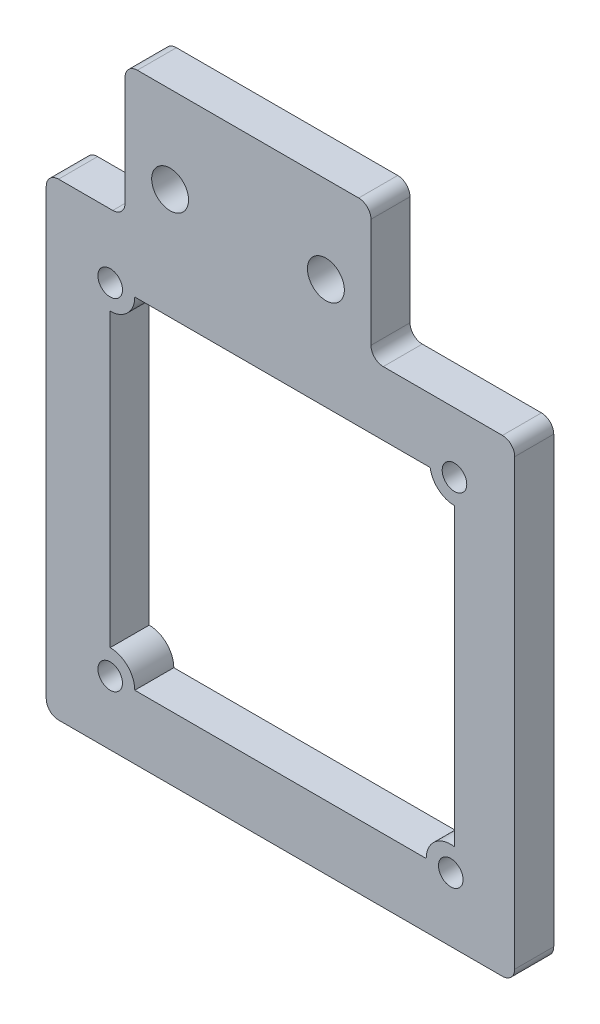
SolidWorks part; units mm, degrees
ref_plane "Front Plane" through (0, 0, 0) normal (0, 0, 1) x (1, 0, 0)
ref_plane "Top Plane" through (0, 0, 0) normal (0, 1, 0) x (1, 0, 0)
ref_plane "Right Plane" through (0, 0, 0) normal (1, 0, 0) x (0, 0, -1)
sketch "Sketch1" plane through (0, 0, 0) normal (0, 0, 1) x (1, 0, 0)
  line L0 (31.6909, -38.1) -> (31.6909, 0) construction
  line L1 (-6.4091, -38.1) -> (31.6909, -38.1) construction
  line L2 (-6.4091, 0) -> (-6.4091, -38.1) construction
  line L3 (31.6909, 0) -> (-6.4091, 0) construction
  line L4 (0, 14.3492) -> (0, 0) construction
  line L5 (16.335, 3.8116) -> (20, 3.8116) construction
  line L6 (20, 14.3492) -> (20, 0) construction
  line L7 (31.6909, -38.1) -> (31.6909, 0)
  line L8 (-6.4091, -38.1) -> (31.6909, -38.1)
  line L9 (-6.4091, 0) -> (-6.4091, -38.1)
  line L10 (31.6909, 0) -> (20, 0)
  line L11 (0, 10.8755) -> (0, 0)
  line L12 (3.665, 3.8116) -> (0, 3.8116) construction
  line L13 (20, 10.8755) -> (20, 0)
  line L14 (0, 0) -> (-6.4091, 0)
  line L15 (20, 10.8755) -> (0, 10.8755)
  line L16 (10, 10.8755) -> (10, -38.1) construction
  line L17 (26.7909, -6.9) -> (26.7909, -30.9226)
  line L18 (24.4909, -32.9) -> (0.7909, -32.9)
  line L19 (-1.2091, -7.2) -> (-1.2091, -30.9)
  line L22 (24.8135, -5.2) -> (0.7909, -5.2)
  circle A3 centre (-1.2091, -5.2) radius 0.7556 construction
  circle A4 centre (26.4909, -32.9) radius 1
  circle A5 centre (-1.2091, -32.9) radius 1
  circle A6 centre (-1.2091, -5.2) radius 1
  circle A7 centre (26.7909, -4.9) radius 1
  circle A8 centre (16.335, 3.8116) radius 1.5
  circle A9 centre (3.665, 3.8116) radius 1.5
  arc A10 (26.7909, -6.9) -> (24.8135, -5.2) centre (26.7909, -4.9) cw
  arc A11 (26.7909, -30.9226) -> (24.4909, -32.9) centre (26.4909, -32.9) ccw
  arc A12 (0.7909, -32.9) -> (-1.2091, -30.9) centre (-1.2091, -32.9) ccw
  arc A13 (-1.2091, -7.2) -> (0.7909, -5.2) centre (-1.2091, -5.2) ccw
  circle A15 centre (-1.2091, -32.9) radius 0.7556 construction
  circle A16 centre (26.4909, -32.9) radius 0.9271 construction
  dimension "D1" = 3
  dimension "D2" = 1
  dimension "D3" = 2
extrude "Boss-Extrude1" add sketch "Sketch1" along normal blind 3.175 contours A5 | A4 | A9 | L13 L10 L7 L8 L9 L14 L11 L15 | L19 A12 L18 A11 L17 A10 L22 A13 | A7 | A6 | A8
fillet "Fillet1" radius 1 8 edges at (20, 0, 1.5875) (20, 10.8755, 1.5875) (0, 10.8755, 1.5875) (0, 0, 1.5875) (-6.4091, 0, 1.5875) (-6.4091, -38.1, 1.5875) (31.6909, 0, 1.5875) (31.6909, -38.1, 1.5875)
